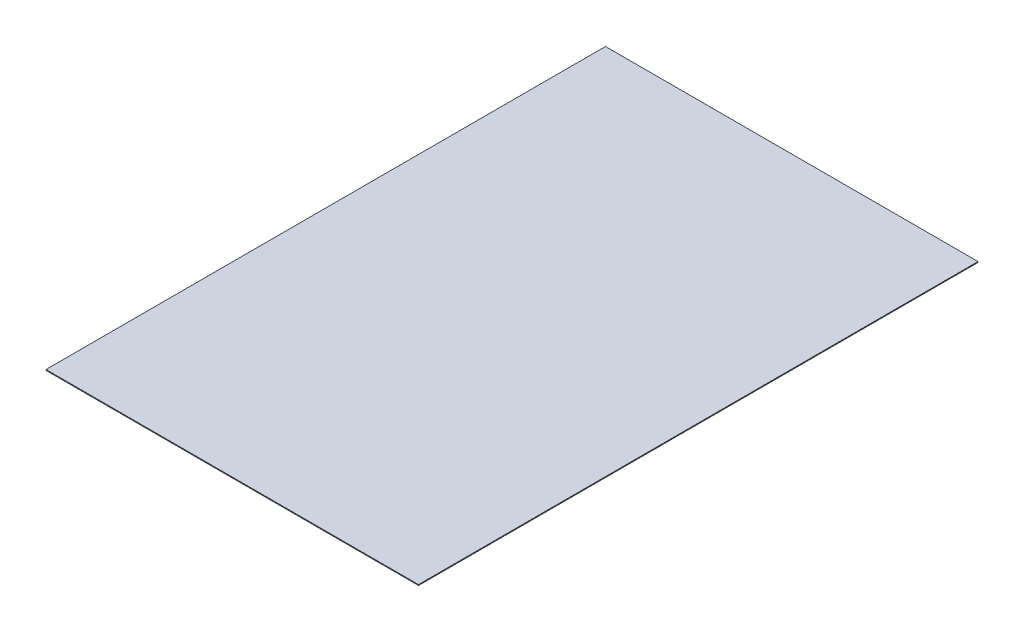
SolidWorks part; units mm, degrees
material "Oak"
ref_plane "Front Plane" through (0, 0, 0) normal (0, 0, 1) x (1, 0, 0)
ref_plane "Top Plane" through (0, 0, 0) normal (0, 1, 0) x (1, 0, 0)
ref_plane "Right Plane" through (0, 0, 0) normal (1, 0, 0) x (0, 0, -1)
sketch "Sketch1" plane through (0, 0, 0) normal (0, 1, 0) x (1, 0, 0)
  line L1 (-6725, 5050) -> (0, 5050)
  line L2 (-6725, 5050) -> (-6725, -5050)
  line L3 (-6725, -5050) -> (0, -5050)
  line L4 (0, 5050) -> (0, -5050)
  dimension "D1" = 6725
  dimension "D2" = 10100
  dimension "D3" = 5050
extrude "Boss-Extrude1" add sketch "Sketch1" against normal blind 15
equation "\"a\" = 6725"
equation "\"D1@Sketch1\"=\"a\""
equation "\"b\"= 10100"
equation "\"D2@Sketch1\"=\"b\""
equation "\"D3@Sketch1\"=\"b\"/2"
